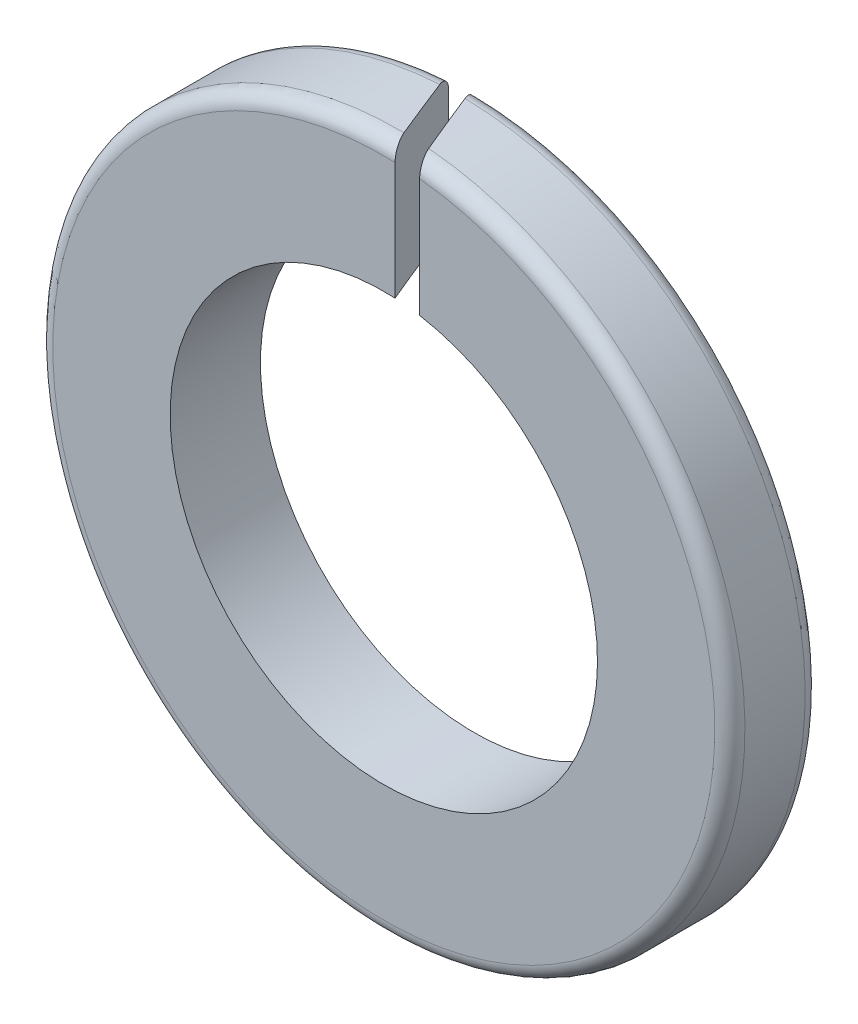
SolidWorks part; units mm, degrees
ref_plane "Face" through (0, 0, 0) normal (0, 0, 1) x (1, 0, 0)
ref_plane "Dessus" through (0, 0, 0) normal (0, 1, 0) x (1, 0, 0)
ref_plane "Droite" through (0, 0, 0) normal (1, 0, 0) x (0, 0, -1)
sketch "Esquisse1" plane through (0, 0, 0) normal (0, 0, 1) x (1, 0, 0)
  circle A0 centre (0, 0) radius 7.1
  circle A1 centre (0, 0) radius 11.5
  dimension "D1" = 23
  dimension "D2" = 14.2
extrude "Extrusion1" add sketch "Esquisse1" along normal blind 3
fillet "Congé2" radius 0.5
sketch "Esquisse2" plane through (0, 0, 0) normal (0, 1, 0) x (1, 0, 0)
  line L0 (-0.8626, 2.1662) -> (1.5366, -3.8722)
  line L1 (-1.7253, 2.1662) -> (0.7278, -3.8722)
  line L2 (0.7278, -3.8722) -> (1.5366, -3.8722)
  line L3 (-1.7253, 2.1662) -> (-0.8626, 2.1662)
extrude "Enlèv. mat.-Extru.1" cut sketch "Esquisse2" along normal through all
